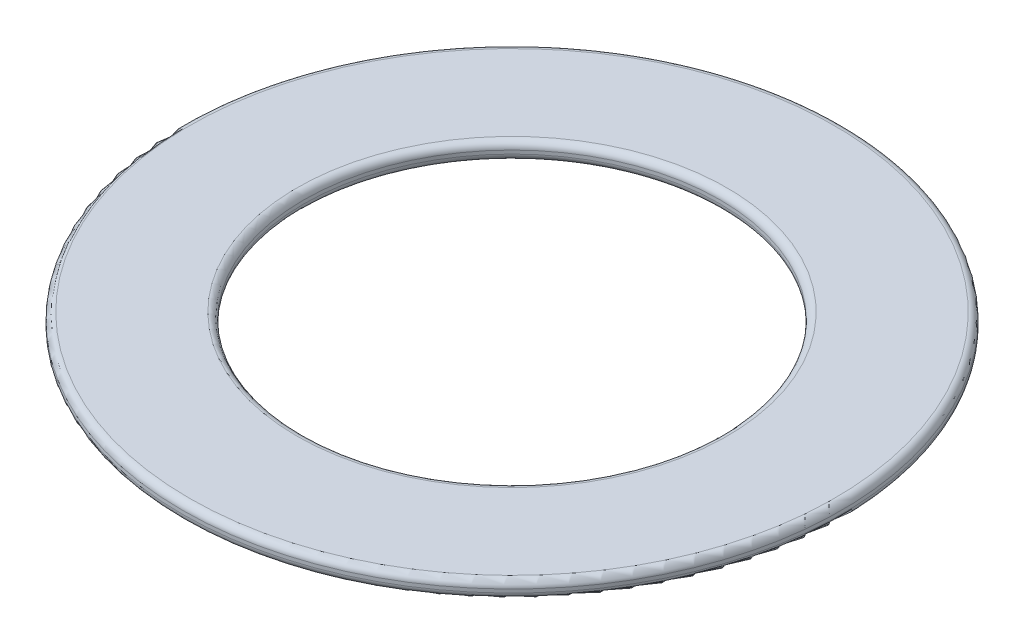
SolidWorks part; units mm, degrees
ref_plane "Front Plane" through (0, 0, 0) normal (0, 0, 1) x (1, 0, 0)
ref_plane "Top Plane" through (0, 0, 0) normal (0, 1, 0) x (1, 0, 0)
ref_plane "Right Plane" through (0, 0, 0) normal (1, 0, 0) x (0, 0, -1)
sketch "Sketch1" plane through (0, 0, 0) normal (0, 1, 0) x (1, 0, 0)
  circle A0 centre (0, 0) radius 9.5
  circle A1 centre (0, 0) radius 6
  dimension "D1" = 19
  dimension "D2" = 12
extrude "Boss-Extrude1" add sketch "Sketch1" along normal blind 0.5
fillet "Fillet1" radius 0.2 4 edges at (0, 0, 6) (0, 0.5, 6) (0, 0, 9.5) (0, 0.5, 9.5)
